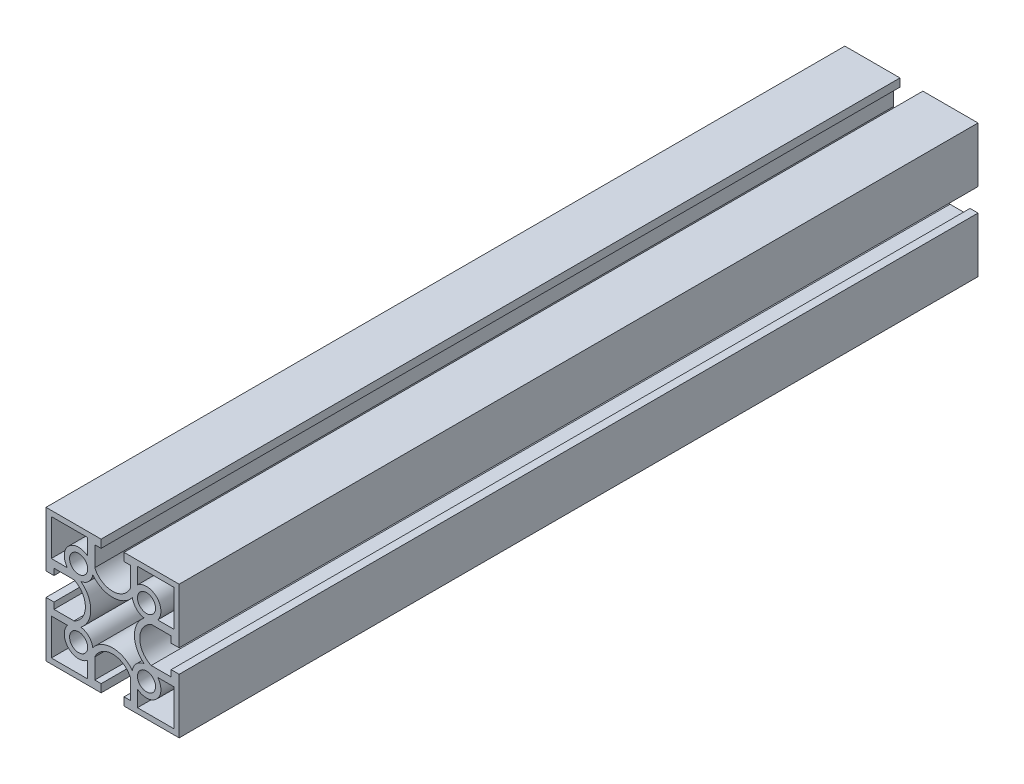
SolidWorks part; units mm, degrees
material "2024-O"
ref_plane "前基準面" through (0, 0, 0) normal (0, 0, 1) x (1, 0, 0)
ref_plane "上基準面" through (0, 0, 0) normal (0, 1, 0) x (1, 0, 0)
ref_plane "右基準面" through (0, 0, 0) normal (1, 0, 0) x (0, 0, -1)
sketch "草圖1" plane through (0, 0, 0) normal (0, 0, 1) x (1, 0, 0)
  line L0 (-26.0983, 0) -> (26.0983, 0) construction
  line L1 (0, -26.0995) -> (0, 26.0995) construction
  line L2 (4.3, 25) -> (25, 25)
  line L3 (25, 25) -> (25, 4.3)
  line L4 (25, 4.3) -> (22, 4.3)
  line L5 (22, 4.3) -> (22, 6.6873)
  line L6 (22, 6.6873) -> (14.5, 6.6873)
  line L7 (4.3, 25) -> (4.3, 22)
  line L8 (6.6873, 22) -> (6.6873, 14.5)
  line L9 (9.35, 23) -> (23, 23)
  line L10 (23, 23) -> (23, 9.35)
  line L11 (23, 9.35) -> (16.9452, 9.35)
  line L12 (9.35, 23) -> (9.35, 16.9452)
  line L13 (4.3, 22) -> (6.6873, 22)
  line L14 (23, 23) -> (23, 25) construction
  line L15 (23, 23) -> (25, 23) construction
  line L16 (18.9804, 25) -> (18.9804, 0) construction
  line L17 (25, 19.6172) -> (0, 19.6172) construction
  line L18 (8.2, -11.115) -> (8.2, 11.115) construction
  line L19 (-1.3349, 8.2958) -> (-1.0493, 10.2753) construction
  line L20 (10.6427, 6.3017) -> (12.1202, 4.9537) construction
  line L21 (12.75, 12.75) -> (12.75, 0) construction
  line L22 (12.75, 12.75) -> (0, 12.75) construction
  line L23 (0, 8.2) -> (4.3078, 8.2) construction
  line L24 (2.8556, 8.2) -> (2.8556, 0) construction
  line L25 (8.2, 4.4271) -> (0, 4.4271) construction
  line L27 (-4.3078, -8.2) -> (4.3078, -8.2) construction
  line L28 (12.75, -12.75) -> (-12.75, -12.75) construction
  line L29 (10.6427, -6.3017) -> (12.1202, -4.9537) construction
  line L30 (-1.3349, -8.2958) -> (-1.0493, -10.2753) construction
  line L31 (25, -19.6172) -> (-25, -19.6172) construction
  line L32 (23, -23) -> (25, -23) construction
  line L33 (23, -23) -> (23, -25) construction
  line L34 (4.3, -22) -> (6.6873, -22)
  line L35 (9.35, -23) -> (9.35, -16.9452)
  line L36 (23, -9.35) -> (16.9452, -9.35)
  line L37 (23, -23) -> (23, -9.35)
  line L38 (9.35, -23) -> (23, -23)
  line L39 (6.6873, -22) -> (6.6873, -14.5)
  line L40 (4.3, -25) -> (4.3, -22)
  line L41 (22, -6.6873) -> (14.5, -6.6873)
  line L42 (22, -4.3) -> (22, -6.6873)
  line L43 (25, -4.3) -> (22, -4.3)
  line L44 (25, -25) -> (25, -4.3)
  line L45 (4.3, -25) -> (25, -25)
  line L46 (-23, -23) -> (-23, -25) construction
  line L47 (-23, -23) -> (-25, -23) construction
  line L48 (1.3349, -8.2958) -> (1.0493, -10.2753) construction
  line L49 (-10.6427, -6.3017) -> (-12.1202, -4.9537) construction
  line L50 (-10.6427, 6.3017) -> (-12.1202, 4.9537) construction
  line L51 (1.3349, 8.2958) -> (1.0493, 10.2753) construction
  line L52 (-8.2, -11.115) -> (-8.2, 11.115) construction
  line L53 (-23, 23) -> (-25, 23) construction
  line L54 (-23, 23) -> (-23, 25) construction
  line L55 (-4.3, -25) -> (-25, -25)
  line L56 (-25, -25) -> (-25, -4.3)
  line L57 (-25, -4.3) -> (-22, -4.3)
  line L58 (-22, -4.3) -> (-22, -6.6873)
  line L59 (-22, -6.6873) -> (-14.5, -6.6873)
  line L60 (-4.3, -25) -> (-4.3, -22)
  line L61 (-6.6873, -22) -> (-6.6873, -14.5)
  line L62 (-9.35, -23) -> (-23, -23)
  line L63 (-23, -23) -> (-23, -9.35)
  line L64 (-23, -9.35) -> (-16.9452, -9.35)
  line L65 (-9.35, -23) -> (-9.35, -16.9452)
  line L66 (-4.3, -22) -> (-6.6873, -22)
  line L67 (-4.3, 22) -> (-6.6873, 22)
  line L68 (-9.35, 23) -> (-9.35, 16.9452)
  line L69 (-23, 9.35) -> (-16.9452, 9.35)
  line L70 (-23, 23) -> (-23, 9.35)
  line L71 (-9.35, 23) -> (-23, 23)
  line L72 (-6.6873, 22) -> (-6.6873, 14.5)
  line L73 (-4.3, 25) -> (-4.3, 22)
  line L74 (-22, 6.6873) -> (-14.5, 6.6873)
  line L75 (-22, 4.3) -> (-22, 6.6873)
  line L76 (-25, 4.3) -> (-22, 4.3)
  line L77 (-25, 25) -> (-25, 4.3)
  line L78 (-4.3, 25) -> (-25, 25)
  arc A0 (6.6873, 14.5) -> (-6.6873, 14.5) centre (0, 17.55) cw
  arc A1 (16.9452, 9.35) -> (9.35, 16.9452) centre (12.75, 12.75) ccw
  circle A2 centre (12.75, 12.75) radius 3.4
  arc A3 (14.5, -6.6873) -> (14.5, 6.6873) centre (17.55, 0) cw
  arc A4 (11.8648, 7.423) -> (11.8648, -7.423) centre (17.55, 0) ccw
  arc A5 (7.423, 11.8648) -> (-7.423, 11.8648) centre (0, 17.55) cw
  arc A6 (7.423, 11.8648) -> (11.8648, 7.423) centre (12.75, 12.75) ccw
  arc A7 (7.423, -11.8648) -> (11.8648, -7.423) centre (12.75, -12.75) cw
  arc A8 (7.423, -11.8648) -> (-7.423, -11.8648) centre (0, -17.55) ccw
  circle A9 centre (12.75, -12.75) radius 3.4
  arc A10 (16.9452, -9.35) -> (9.35, -16.9452) centre (12.75, -12.75) cw
  arc A11 (6.6873, -14.5) -> (-6.6873, -14.5) centre (0, -17.55) ccw
  arc A12 (-16.9452, -9.35) -> (-9.35, -16.9452) centre (-12.75, -12.75) ccw
  circle A13 centre (-12.75, -12.75) radius 3.4
  arc A14 (-7.423, -11.8648) -> (-11.8648, -7.423) centre (-12.75, -12.75) ccw
  arc A15 (-7.423, 11.8648) -> (-11.8648, 7.423) centre (-12.75, 12.75) cw
  arc A16 (-11.8648, 7.423) -> (-11.8648, -7.423) centre (-17.55, 0) cw
  arc A17 (-14.5, -6.6873) -> (-14.5, 6.6873) centre (-17.55, 0) ccw
  circle A18 centre (-12.75, 12.75) radius 3.4
  arc A19 (-16.9452, 9.35) -> (-9.35, 16.9452) centre (-12.75, 12.75) cw
  point P51 (2.8725, 0)
  point P55 (12.725, 0)
  point P63 (20.8598, 0)
  point P88 (0, -19.6172)
  point P93 (0, -12.75)
  point P95 (0, -2.988)
  point P96 (0, 2.988)
  point P106 (0, 0)
  point P137 (-20.8598, 0)
  point P138 (-12.725, 0)
  point P139 (-2.8725, 0)
  dimension "D4" = 2
  dimension "D8" = 2
  dimension "D9" = 6.8
  dimension "D1" = 25
  dimension "D2" = 8.6
  dimension "D3" = 3
  dimension "D5" = 2
  dimension "D6" = 7.5
  dimension "D7" = 8.2
  dimension "D10" = 25.5
extrude "本體" add sketch "草圖1" along normal mid plane 300
sketch "草圖2" [suppressed] plane through (25, 0, 0) normal (1, 0, 0) x (0, 0, -1)
  line L1 (-750, 4.3) -> (-750, 25) construction
  circle A0 centre (-736, 0) radius 4
  circle A2 centre (-736, 0) radius 14 construction
  dimension "D1" = 8
  dimension "D2" = 10
extrude "馬達架孔1" [suppressed] cut sketch "草圖2" against normal through all
pattern_linear "馬達架孔N" [suppressed] count 4 spacing 50
